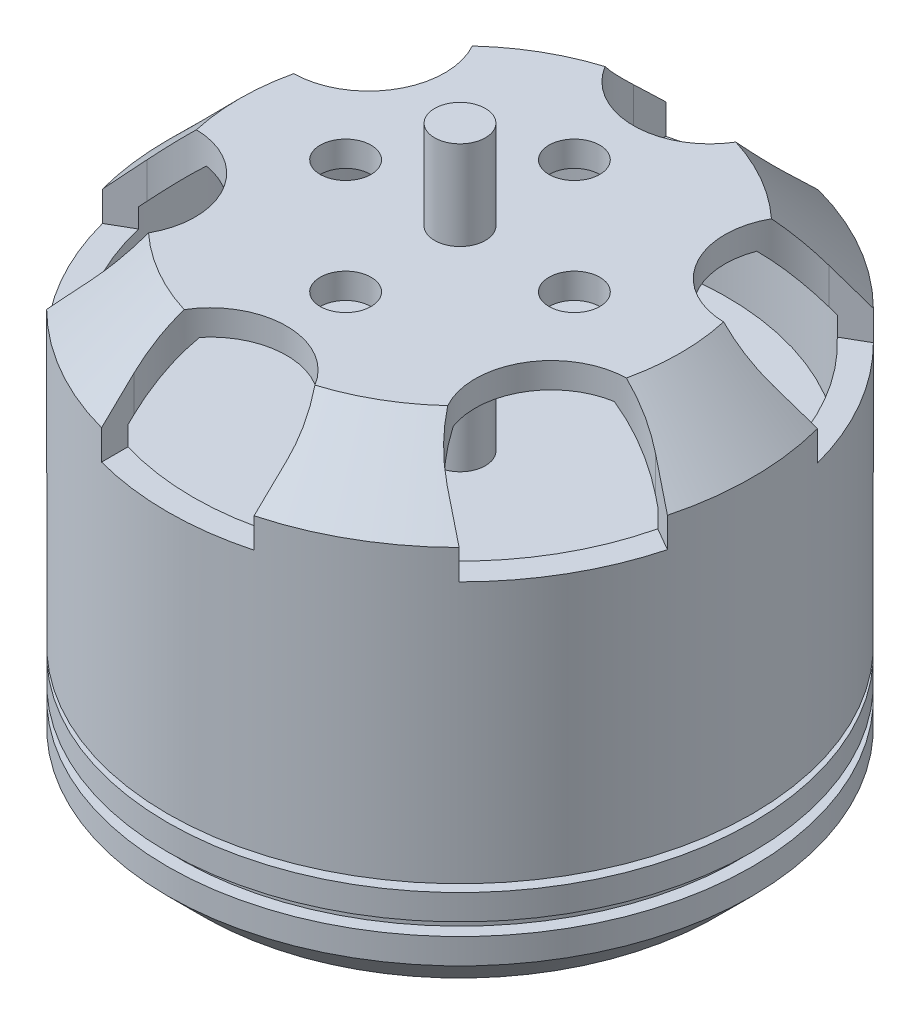
SolidWorks part; units mm, degrees
ref_plane "Front Plane" through (0, 0, 0) normal (0, 0, 1) x (1, 0, 0)
ref_plane "Top Plane" through (0, 0, 0) normal (0, 1, 0) x (1, 0, 0)
ref_plane "Right Plane" through (0, 0, 0) normal (1, 0, 0) x (0, 0, -1)
sketch "Sketch1" plane through (0, 0, 0) normal (0, 0, 1) x (1, 0, 0)
  line L0 (0, 21.6427) -> (0, 0)
  line L1 (1, -0.3573) -> (10.0858, -0.3573)
  line L2 (10.0858, -0.3573) -> (11.5, 1.0569)
  line L3 (11.5, 1.0569) -> (11.5, 2.0569)
  line L4 (11.5, 15.3143) -> (8.6716, 18.1427)
  line L5 (8.6716, 18.1427) -> (1, 18.1427)
  line L6 (1, 18.1427) -> (1, 21.6427)
  line L7 (1, 21.6427) -> (0, 21.6427)
  line L8 (0, 0) -> (0, -2.1573)
  line L9 (0, -2.1573) -> (1, -2.1573)
  line L10 (1, -2.1573) -> (1, -0.3573)
  line L11 (2, 17.1427) -> (8.2574, 17.1427)
  line L12 (8.2574, 17.1427) -> (10.5, 14.9001)
  line L13 (10.5, 14.9001) -> (10.5, 10.4677)
  line L14 (10.5, 10.4677) -> (1, 10.4677)
  line L15 (1, 10.4677) -> (1, 16.1427)
  line L16 (1, 16.1427) -> (2, 16.1427)
  line L17 (2, 16.1427) -> (2, 17.1427)
  line L18 (11.5, 2.0569) -> (11, 2.0569)
  line L19 (11, 2.0569) -> (11, 2.5569)
  line L20 (11, 2.5569) -> (11.5, 2.5569)
  line L21 (11.5, 3.5569) -> (9.5, 3.5569)
  line L22 (9.5, 3.5569) -> (9.5, 3.8569)
  line L23 (9.5, 3.8569) -> (11.5, 3.8569)
  line L24 (11.5, 2.5569) -> (11.5, 3.5569)
  line L25 (11.5, 3.8569) -> (11.5, 15.3143)
  point P3 (0.5, 21.6427)
  point P13 (1, 13.3052)
  dimension "D1" = 23.8
  dimension "D2" = 1.8
  dimension "D3" = 45
  dimension "D4" = 2
  dimension "D5" = 1
  dimension "D6" = 1
  dimension "D7" = 11.5
  dimension "D8" = 3.5
  dimension "D9" = 45
  dimension "D10" = 1
  dimension "D11" = 1
  dimension "D12" = 1
  dimension "D13" = 1
  dimension "D14" = 1
  dimension "D15" = 1
  dimension "D16" = 4
  dimension "D17" = 0.5
  dimension "D18" = 0.5
  dimension "D19" = 1
  dimension "D20" = 1
  dimension "D21" = 0.3
  dimension "D22" = 2
revolve "Revolve1" add sketch "Sketch1" angle 360 about L0
sketch "Sketch2" plane through (0, 18.1427, 0) normal (0, 1, 0) x (1, 0, 0)
  line L0 (0, 0) -> (0, 9) construction
  line L1 (-3, 9.8245) -> (-3, 15.5473)
  line L2 (-3, 15.5473) -> (3, 15.5473)
  line L3 (3, 15.5473) -> (3, 9.8245)
  line L4 (11.9644, 10.3717) -> (14.9644, 5.1756)
  line L5 (14.9644, 5.1756) -> (10.0083, 2.3142)
  line L6 (7.0083, 7.5103) -> (11.9644, 10.3717)
  line L7 (14.9644, -5.1756) -> (11.9644, -10.3717)
  line L8 (11.9644, -10.3717) -> (7.0083, -7.5103)
  line L9 (10.0083, -2.3142) -> (14.9644, -5.1756)
  line L10 (3, -15.5473) -> (-3, -15.5473)
  line L11 (-3, -15.5473) -> (-3, -9.8245)
  line L12 (3, -9.8245) -> (3, -15.5473)
  line L13 (-11.9644, -10.3717) -> (-14.9644, -5.1756)
  line L14 (-14.9644, -5.1756) -> (-10.0083, -2.3142)
  line L15 (-7.0083, -7.5103) -> (-11.9644, -10.3717)
  line L16 (-14.9644, 5.1756) -> (-11.9644, 10.3717)
  line L17 (-11.9644, 10.3717) -> (-7.0083, 7.5103)
  line L18 (-10.0083, 2.3142) -> (-14.9644, 5.1756)
  circle A0 centre (0, 0) radius 4.5 construction
  circle A1 centre (0, 0) radius 9.4387 construction
  circle A2 centre (0, -4.5) radius 1
  circle A3 centre (-4.5, 0) radius 1
  circle A4 centre (0, 4.5) radius 1
  circle A5 centre (4.5, 0) radius 1
  arc A6 (-3, 9.8245) -> (3, 9.8245) centre (0, 9.8245) ccw
  arc A7 (7.0083, 7.5103) -> (10.0083, 2.3142) centre (8.5083, 4.9122) ccw
  arc A8 (10.0083, -2.3142) -> (7.0083, -7.5103) centre (8.5083, -4.9122) ccw
  arc A9 (3, -9.8245) -> (-3, -9.8245) centre (0, -9.8245) ccw
  arc A10 (-7.0083, -7.5103) -> (-10.0083, -2.3142) centre (-8.5083, -4.9122) ccw
  arc A11 (-10.0083, 2.3142) -> (-7.0083, 7.5103) centre (-8.5083, 4.9122) ccw
  point P16 (0, 0)
  point P46 (0, 0)
  dimension "D1" = 9
  dimension "D3" = 2
  dimension "D5" = 6
  dimension "D2" = 9
  dimension "D4" = 4
  dimension "D6" = 6
extrude "Cut-Extrude1" cut sketch "Sketch2" against normal blind 4
sketch "Sketch3" plane through (0, -0.3573, 0) normal (0, -1, 0) x (1, 0, 0)
  circle A0 centre (0, 0) radius 6 construction
  circle A1 centre (0, 0) radius 8 construction
  circle A2 centre (0, -6) radius 1
  circle A3 centre (0, 6) radius 1
  circle A4 centre (-8, 0) radius 1
  circle A5 centre (8, 0) radius 1
  dimension "D1" = 12
  dimension "D2" = 16
  dimension "D3" = 2
extrude "Cut-Extrude2" cut sketch "Sketch3" against normal blind 3
